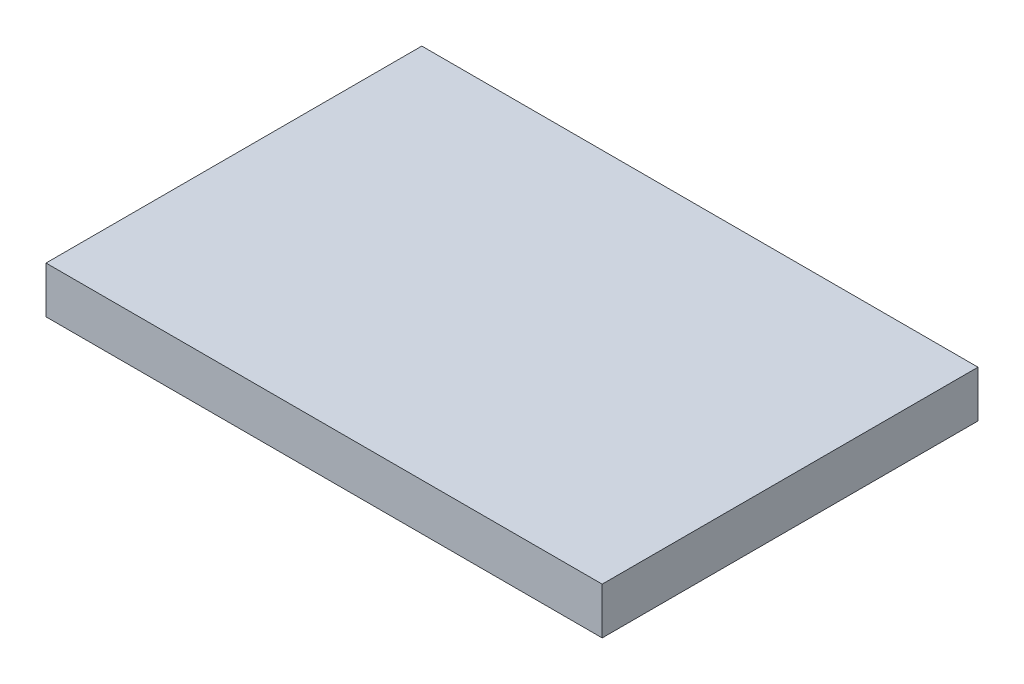
SolidWorks part; units mm, degrees
ref_plane "Front Plane" through (0, 0, 0) normal (0, 0, 1) x (1, 0, 0)
ref_plane "Top Plane" through (0, 0, 0) normal (0, 1, 0) x (1, 0, 0)
ref_plane "Right Plane" through (0, 0, 0) normal (1, 0, 0) x (0, 0, -1)
sketch "Sketch1" plane through (0, 0, 0) normal (0, 1, 0) x (1, 0, 0)
  line L1 (92.5, -62.5) -> (-92.5, -62.5)
  line L2 (92.5, -62.5) -> (92.5, 62.5)
  line L3 (92.5, 62.5) -> (-92.5, 62.5)
  line L4 (-92.5, -62.5) -> (-92.5, 62.5)
  line L5 (92.5, -62.5) -> (-92.5, 62.5) construction
  line L6 (92.5, 62.5) -> (-92.5, -62.5) construction
  point P0 (0, 0)
  dimension "D1" = 125
  dimension "D2" = 185
extrude "Boss-Extrude1" add sketch "Sketch1" along normal blind 15.5
